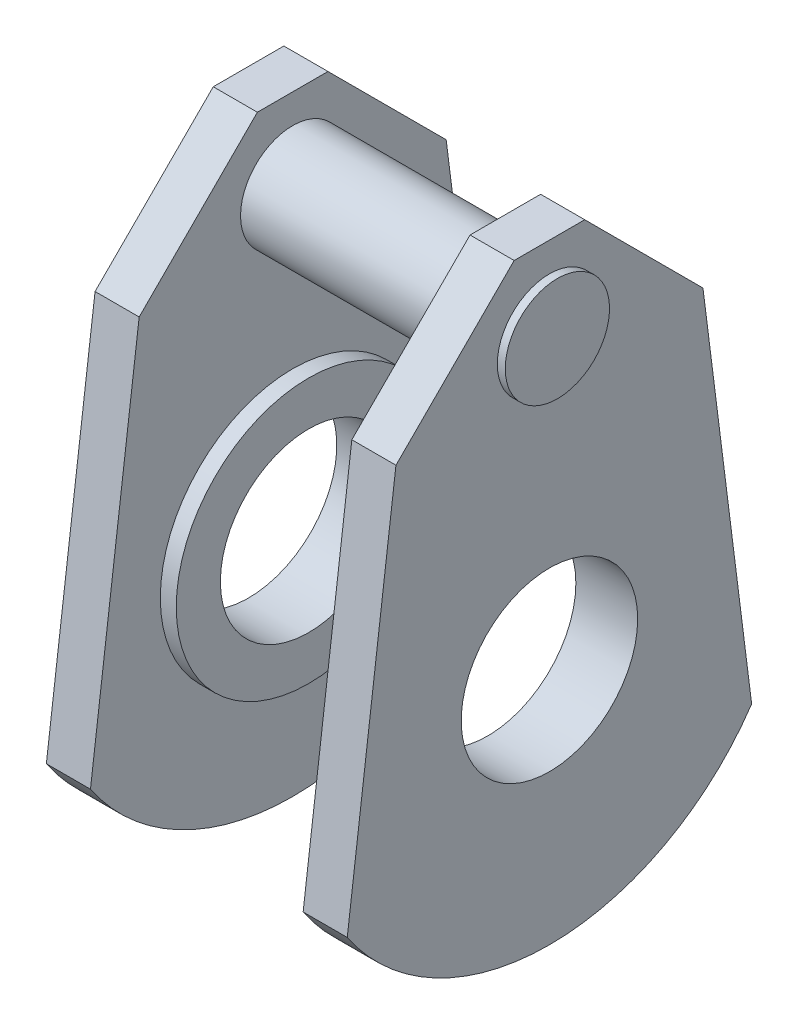
SolidWorks part; units mm, degrees
ref_plane "Ön Düzlem" through (0, 0, 0) normal (0, 0, 1) x (1, 0, 0)
ref_plane "Üst Düzlem" through (0, 0, 0) normal (0, 1, 0) x (1, 0, 0)
ref_plane "Sağ Düzlem" through (0, 0, 0) normal (1, 0, 0) x (0, 0, -1)
sketch "Çizim2" plane through (0, 0, 0) normal (1, 0, 0) x (0, 0, -1)
  circle A0 centre (0, 0) radius 10
  circle A1 centre (0, 0) radius 15
extrude "Yükseklik-Ekstrüzyon1" add sketch "Çizim2" along normal mid plane 24.1 contours A1 | A0
sketch "Çizim3" plane through (12.05, 0, 0) normal (1, 0, 0) x (0, 0, -1)
  line L0 (0, -1053.9813) -> (0, -26.9907) construction
  line L1 (-4, 42.1769) -> (4, 42.1769)
  line L2 (-4, 42.1769) -> (-17.3956, 28.7813)
  line L3 (-17.3956, 28.7813) -> (-22.9145, -14.8053)
  line L4 (17.3956, 28.7813) -> (22.9145, -14.8053)
  line L5 (4, 42.1769) -> (17.3956, 28.7813)
  line L6 (0, 42.1769) -> (0, 1042.9767) construction
  arc A0 (-22.9145, -14.8053) -> (22.9145, -14.8053) centre (0, 0.6473) ccw
  circle A1 centre (0, 0) radius 10 construction
  circle A2 centre (0, 0) radius 10
  point P6 (0, 42.1769)
extrude "Yükseklik-Ekstrüzyon2" add sketch "Çizim3" along normal blind 5
sketch "Çizim4" plane through (-12.05, 0, 0) normal (-1, 0, 0) x (0, 0, 1)
  line L0 (-4, 42.1769) -> (4, 42.1769) construction
  line L1 (4, 42.1769) -> (17.3956, 28.7813) construction
  line L2 (17.3956, 28.7813) -> (22.9145, -14.8053) construction
  line L3 (-22.9145, -14.8053) -> (-17.3956, 28.7813) construction
  line L4 (-17.3956, 28.7813) -> (-4, 42.1769) construction
  line L5 (-4, 42.1769) -> (4, 42.1769)
  line L6 (4, 42.1769) -> (17.3956, 28.7813)
  line L7 (17.3956, 28.7813) -> (22.9145, -14.8053)
  line L8 (-22.9145, -14.8053) -> (-17.3956, 28.7813)
  line L9 (-17.3956, 28.7813) -> (-4, 42.1769)
  arc A0 (-22.9145, -14.8053) -> (22.9145, -14.8053) centre (0, 0.6473) ccw construction
  circle A1 centre (0, 0) radius 15
  circle A2 centre (0, 0) radius 15
  arc A3 (-22.9145, -14.8053) -> (22.9145, -14.8053) centre (0, 0.6473) ccw
  dimension "D1" = 0
extrude "Yükseklik-Ekstrüzyon3" add sketch "Çizim4" along normal blind 5 separate body
sketch "Çizim5" plane through (-17.05, 0, 0) normal (-1, 0, 0) x (0, 0, 1)
  line L0 (0, 42.1769) -> (0, 32.4152) construction
  line L1 (4, 42.1769) -> (-4, 42.1769) construction
  circle A0 centre (0, 32.9574) radius 5.907
sketch "Çizim7" plane through (-12.05, 0, 0) normal (-1, 0, 0) x (0, 0, 1)
  circle A0 centre (0, 0) radius 15
  circle A1 centre (0, 0) radius 10
extrude "Yükseklik-Ekstrüzyon4" add sketch "Çizim7" along normal blind 5
extrude "Yükseklik-Ekstrüzyon5" add sketch "Çizim5" along normal blind 1 and the other way blind 35 contours A0
sketch "Çizim8" plane through (0, 0, 0) normal (0, 0, 1) x (1, 0, 0)
  line L0 (-12.05, 14.9423) -> (12.05, 15)
  line L1 (-12.05, 14.9423) -> (-11.9835, -12.8344)
  line L2 (12.05, 15) -> (12.1165, -12.7768)
  line L3 (-11.9835, -12.8344) -> (12.1165, -12.7768)
  line L4 (-12.05, -14.8053) -> (-12.05, 28.7813) construction
ref_plane "Düzlem1" through (0, 0, 68.7606) normal (0, 0, 1) x (1, 0, 0)
sketch "Çizim9" plane through (0, 0, 68.7606) normal (0, 0, 1) x (1, 0, 0)
  line L0 (-12.05, 14.9423) -> (12.05, 15)
  line L1 (-12.05, 14.9423) -> (-11.9793, -14.6186)
  line L2 (12.05, 15) -> (12.1207, -14.561)
  line L3 (-11.9793, -14.6186) -> (12.1207, -14.561)
sketch "Sketch1" plane through (0, 0, 68.7606) normal (0, 0, 1) x (1, 0, 0)
  line L1 (-10.2436, 16.5756) -> (10.0427, 16.5756)
  line L2 (-10.2436, 16.5756) -> (-10.2436, -24.1988)
  line L3 (-10.2436, -24.1988) -> (10.0427, -24.1988)
  line L4 (10.0427, 16.5756) -> (10.0427, -24.1988)
extrude "Cut-Extrude1" cut sketch "Sketch1" against normal blind 110
